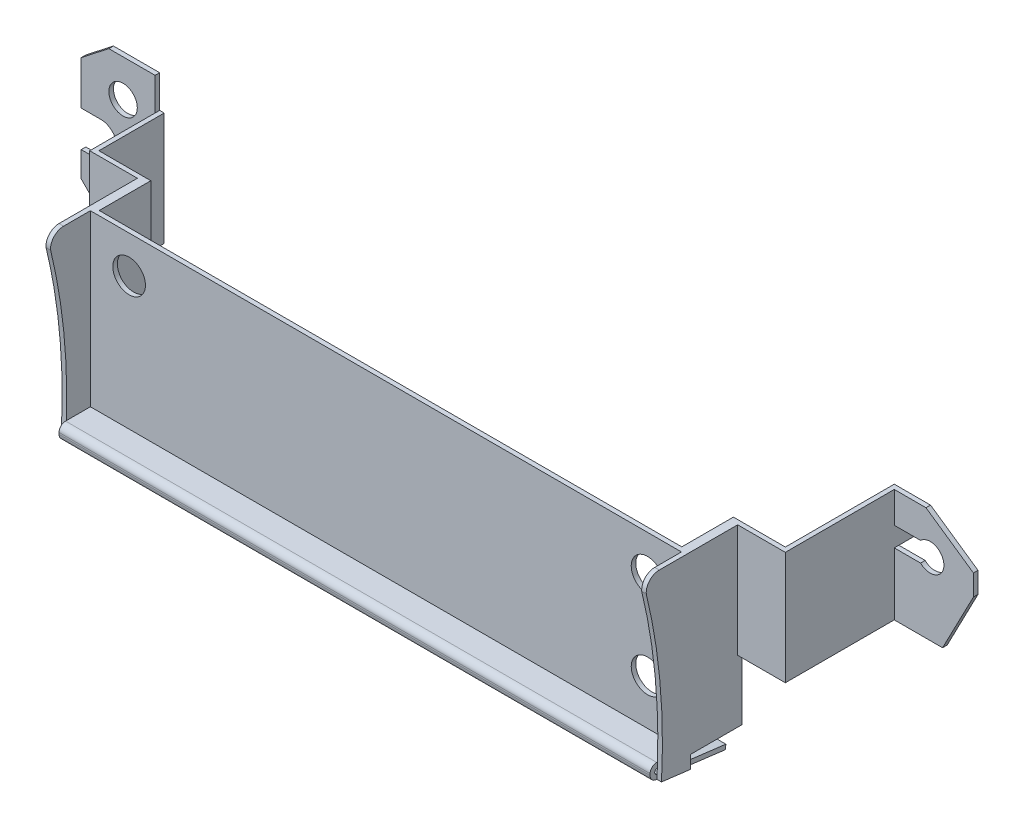
SolidWorks part; units mm, degrees
ref_plane "Front" through (0, 0, 0) normal (0, 0, 1) x (1, 0, 0)
ref_plane "Top" through (0, 0, 0) normal (0, 1, 0) x (1, 0, 0)
ref_plane "Right" through (0, 0, 0) normal (1, 0, 0) x (0, 0, -1)
sketch "Szkic1" plane through (0, 0, 0) normal (0, 0, 1) x (1, 0, 0)
  line L0 (-36.3541, -25.4134) -> (54.1459, -25.4134)
  line L1 (8.8959, -25.4134) -> (8.8959, 3.5933) construction
  line L2 (-36.3541, 0.5866) -> (54.1459, 0.5866)
  line L3 (-36.3541, 0.5866) -> (-36.3541, -25.4134)
  line L4 (54.1459, 0.5866) -> (54.1459, -25.4134)
  dimension "D1" = 26
  dimension "D3" = 90.5
  dimension "D2" = 26
  dimension "D4" = 90.5
  dimension "D5" = 90
  dimension "D6" = 90
extrude "Dodanie-wyciągnięcie1" add sketch "Szkic1" along normal blind 0.7
sketch "Szkic3" plane through (-36.3541, 0, 0) normal (-1, 0, 0) x (0, 0, 1)
  line L0 (0.7, -25.4134) -> (5.5, -25.4134) construction
  line L1 (0.7, -25.4134) -> (0.7, -28.153) construction
  line L2 (5.5, -26.4134) -> (5.5, -26.6702)
  line L3 (4.624, -27.6625) -> (-6.0104, -28.9918)
  line L4 (-6.0104, -28.9918) -> (-6.0972, -28.2972)
  line L5 (4.8, -26.598) -> (4.8, -26.6355)
  line L6 (-6.0972, -28.2972) -> (4.4976, -26.9779)
  line L7 (4.455, -26.253) -> (0, -26.253)
  line L8 (0, -26.253) -> (0, -25.4134)
  line L9 (0, -25.4134) -> (4.5, -25.4134)
  arc A0 (4.5, -25.4134) -> (5.5, -26.4134) centre (4.5, -26.4134) cw
  arc A1 (5.5, -26.6702) -> (4.624, -27.6625) centre (4.5, -26.6702) cw
  arc A2 (4.8, -26.6355) -> (4.4976, -26.9779) centre (4.455, -26.6355) cw
  arc A3 (4.8, -26.598) -> (4.455, -26.253) centre (4.455, -26.598) ccw
  dimension "D1" = 90
  dimension "D2" = 1
  dimension "D3" = 0.345
extrude "Dodanie-wyciągnięcie2" add sketch "Szkic3" against normal up to surface (90.5 mm away) separate body up to face at (54.1459, -12.4134, 0.35)
sketch "Szkic4" plane through (54.1459, 0, 0) normal (1, 0, 0) x (0, 0, -1)
  line L2 (0, 0.5866) -> (-4.7969, 0.5866)
  line L3 (0, 0.5866) -> (0, -28.2405)
  line L4 (-4.4693, -27.6819) -> (0, -28.2405)
  arc A0 (-6.7876, -1.6062) -> (-4.7969, 0.5866) centre (-4.7969, -1.4134) cw
  spline S0 degree 3 poles (-4.4693, -27.6819) (-4.4425, -27.2049) (-4.0104, -18.29) (-4.8511, -9.6107) (-6.7876, -1.6062) knots -0.045929 -0.045929 -0.045929 -0.045929 0 0.813756 0.813756 0.813756 0.813756
  dimension "D1" = 2
extrude "Dodanie-wyciągnięcie3" add sketch "Szkic4" along normal blind 0.7
sketch "Szkic8" plane through (-36.3541, 0, 0) normal (-1, 0, 0) x (0, 0, 1)
  line L1 (4.4693, -27.6819) -> (0, -28.2405)
  line L2 (4.7969, 0.5866) -> (0, 0.5866)
  line L3 (0, 0.5866) -> (0, -28.2405)
  arc A1 (6.7876, -1.6062) -> (4.7969, 0.5866) centre (4.7969, -1.4134) ccw
  spline S1 degree 3 poles (4.4693, -27.6819) (4.4425, -27.2049) (4.0104, -18.29) (4.8511, -9.6107) (6.7876, -1.6062) knots -0.045929 -0.045929 -0.045929 -0.045929 0 0.813756 0.813756 0.813756 0.813756
extrude "Dodanie-wyciągnięcie4" add sketch "Szkic8" along normal blind 0.7
sketch "Szkic9" plane through (0, 0, 0) normal (0, 0, -1) x (-1, 0, 0)
  line L0 (-54.8459, 0.5866) -> (-54.8459, -26.253)
  line L1 (37.0541, 0.5866) -> (37.0541, -26.253)
  line L2 (-53.4959, 0.5866) -> (-53.4959, -26.253)
  line L3 (-54.1459, -26.253) -> (36.3541, -26.253) construction
  line L4 (-53.4959, -26.253) -> (-54.8459, -26.253)
  line L5 (-54.8459, -28.2405) -> (-54.8459, 0.5866) construction
  line L6 (35.7041, 0.5866) -> (37.0541, 0.5866)
  line L7 (-54.8459, 0.5866) -> (-53.4959, 0.5866)
  line L10 (35.7041, -26.253) -> (37.0541, -26.253)
  line L11 (35.7041, -26.253) -> (35.7041, 0.5866)
extrude "Dodanie-wyciągnięcie5" add sketch "Szkic9" along normal blind 7.9
sketch "Szkic11" plane through (0, 0.5866, 0) normal (0, 1, 0) x (1, 0, 0)
  line L0 (-37.0541, 7.9) -> (-37.0541, 7.2)
  line L1 (-37.0541, 7.2) -> (-44.3541, 7.2)
  line L2 (-44.3541, 7.2) -> (-44.3541, 17.2)
  line L3 (-43.6541, 7.9) -> (-37.0541, 7.9)
  line L4 (-43.6541, 7.9) -> (-43.6541, 17.9)
  line L5 (-55.6541, 17.2) -> (-44.3541, 17.2)
  line L6 (-43.6541, 17.9) -> (-55.6541, 17.9)
  line L7 (-55.6541, 17.9) -> (-55.6541, 17.2)
  dimension "D1" = 10
  dimension "D2" = 11.3
extrude "Dodanie-wyciągnięcie6" add sketch "Szkic11" against normal blind 17.3
sketch "Szkic12" plane through (0, 0.5866, 0) normal (0, 1, 0) x (1, 0, 0)
  line L0 (54.8459, 7.9) -> (54.8459, 7.2)
  line L1 (62.1459, 7.2) -> (54.8459, 7.2)
  line L3 (54.8459, 7.9) -> (61.4459, 7.9)
  line L8 (74.2659, 24.58) -> (74.2659, 23.88)
  line L9 (61.4459, 24.58) -> (74.2659, 24.58)
  line L10 (74.2659, 23.88) -> (62.1459, 23.88)
  line L11 (62.1459, 7.2) -> (62.1459, 23.88)
  line L12 (61.4459, 7.9) -> (61.4459, 24.58)
  dimension "D1" = 12.82
  dimension "D2" = 16.68
  dimension "D3" = 0.7
  dimension "D4" = 16.68
extrude "Dodanie-wyciągnięcie7" add sketch "Szkic12" against normal blind 17.3
sketch "Szkic13" plane through (0, 0, -23.88) normal (0, 0, 1) x (1, 0, 0)
  line L0 (74.2459, -15.1844) -> (74.2459, 4.2987) construction
  line L1 (61.4459, -16.7134) -> (61.4459, 0.5866) construction
  line L2 (76.2499, -4.4134) -> (92.0698, -4.4134) construction
  line L3 (62.1459, 0.5866) -> (74.2659, 0.5866) construction
  line L4 (67.0047, 0.5866) -> (75.4895, -5.2721)
  line L5 (69.5395, -16.7134) -> (76.2499, -16.7134)
  line L6 (76.2499, -16.7134) -> (76.2499, 0.5866)
  line L7 (69.5395, -16.7134) -> (75.4895, -5.2721)
  line L8 (67.0047, 0.5866) -> (76.2499, 0.5866)
  line L10 (62.1459, -4.1634) -> (66.1762, -4.1634)
  line L11 (62.1459, -4.1634) -> (62.1459, -7.1634)
  line L13 (62.1459, -7.1634) -> (66.1762, -7.1634)
  line L14 (69.7459, -1.3062) -> (69.7459, 6.074) construction
  line L15 (62.1459, -5.6634) -> (70.5807, -5.6634) construction
  line L16 (67.6459, -5.6634) -> (69.7459, -5.6634) construction
  circle A0 centre (74.2459, -4.4134) radius 3.25 construction
  arc A1 (66.1762, -7.1634) -> (66.1762, -4.1634) centre (67.6459, -5.6634) ccw
  dimension "D3" = 4.75
  dimension "D1" = 12.8
  dimension "D2" = 5
  dimension "D4" = 3
  dimension "D5" = 7.6
extrude "Wytnij-wyciągnięcie1" cut sketch "Szkic13" against normal up to next
sketch "Szkic14" plane through (0, 0, -24.58) normal (0, 0, -1) x (-1, 0, 0)
  line L0 (-62.1459, -4.1634) -> (-61.4459, -4.1634)
  line L1 (-61.4459, -16.7134) -> (-61.4459, 0.5866) construction
  line L2 (-61.4459, -4.1634) -> (-61.4459, -7.1634)
  line L3 (-62.1459, -7.1634) -> (-62.1459, -4.1634)
  line L4 (-62.1459, -7.1634) -> (-61.4459, -7.1634)
extrude "Dodanie-wyciągnięcie8" add sketch "Szkic14" along normal blind 3.15
sketch "Szkic17" plane through (0, 0, -17.2) normal (0, 0, 1) x (1, 0, 0)
  line L0 (-44.3533, 0.5421) -> (-55.6541, 0.5866)
  line L1 (-55.6541, 0.5866) -> (-55.6541, 5.5866)
  line L2 (-55.6541, 5.5866) -> (-44.3533, 5.5866)
  line L3 (-44.3533, 5.5866) -> (-44.3533, 0.5421)
extrude "Dodanie-wyciągnięcie9" add sketch "Szkic17" against normal up to surface (0.7 mm away) up to face at (-49.6541, -8.0634, -17.9)
sketch "Szkic18" plane through (0, 0, -17.2) normal (0, 0, 1) x (1, 0, 0)
  line L0 (-51.4241, 5.5866) -> (-55.6541, 2.2866)
  line L1 (-51.4241, 5.5866) -> (-55.6541, 5.5866)
  line L2 (-55.6541, 5.5866) -> (-55.6541, 2.2866)
  line L3 (-55.6541, -4.4134) -> (-52.6541, -4.4134)
  line L4 (-55.6541, -16.7134) -> (-55.6541, 5.5866) construction
  line L5 (-44.3533, 5.5866) -> (-55.6541, 5.5866) construction
  line L6 (-55.6541, -9.9134) -> (-52.6541, -9.9134)
  line L7 (-50.1541, -6.9134) -> (-50.1541, -7.4134)
  line L8 (-46.3544, 2.0866) -> (-52.3533, 2.0866) construction
  line L9 (-51.4241, -1.0354) -> (-51.4241, 8.3952) construction
  line L10 (-51.4241, -0.0884) -> (-47.5597, -0.0884) construction
  line L11 (-49.2491, 2.0866) -> (-49.2491, -0.9265) construction
  line L12 (-55.6541, -9.9134) -> (-55.6541, -4.4134)
  arc A0 (-50.1541, -7.4134) -> (-52.6541, -9.9134) centre (-52.6541, -7.4134) cw
  arc A1 (-50.1541, -6.9134) -> (-52.6541, -4.4134) centre (-52.6541, -6.9134) ccw
  circle A2 centre (-49.2491, -0.0884) radius 2.175
  point P16 (-50.1541, -7.1634)
  dimension "D1" = 10
  dimension "D4" = 2.5
  dimension "D2" = 5.5
  dimension "D3" = 5.5
  dimension "D5" = 3.5
  dimension "D6" = 4.23
extrude "Wytnij-wyciągnięcie2" cut sketch "Szkic18" against normal up to surface (0.7 mm away) up to face at (-47.8871, -3.5134, -17.9)
sketch "Szkic19" plane through (0, 0, -17.2) normal (0, 0, 1) x (1, 0, 0)
  line L0 (-55.6541, -16.7134) -> (-55.6541, -18.7134)
  line L1 (-55.6541, -16.7134) -> (-47.1541, -16.7134)
  line L3 (-47.1541, -18.7134) -> (-55.6541, -18.7134)
  line L4 (-47.1541, -16.7134) -> (-47.1541, -18.7134)
extrude "Dodanie-wyciągnięcie10" add sketch "Szkic19" against normal up to surface (0.7 mm away) up to face at (-50.3566, -4.7519, -17.9)
sketch "Szkic21" plane through (0, 0, -17.2) normal (0, 0, 1) x (1, 0, 0)
  line L0 (-55.6541, -13.8134) -> (-50.7541, -18.7134)
  line L1 (-50.7541, -18.7134) -> (-55.6541, -18.7134)
  line L2 (-55.6541, -18.7134) -> (-55.6541, -13.8134)
extrude "Wytnij-wyciągnięcie3" cut sketch "Szkic21" against normal up to surface (0.7 mm away) up to face at (-49.9296, -6.6134, -17.9)
sketch "Szkic22" plane through (0, 0, -17.9) normal (0, 0, -1) x (-1, 0, 0)
  line L0 (47.1541, -18.7134) -> (47.1541, -18.0134)
  line L1 (47.1541, -18.7134) -> (47.1541, -16.7134) construction
  line L3 (47.1541, -18.7134) -> (50.7541, -18.7134)
  line L4 (47.1541, -18.0134) -> (50.7541, -18.0134)
  line L5 (50.7541, -18.7134) -> (50.7541, -18.0134)
extrude "Dodanie-wyciągnięcie11" add sketch "Szkic22" along normal blind 3.3
sketch "Szkic23" plane through (0, 0, 0) normal (0, 0, -1) x (-1, 0, 0)
  line L0 (30.4241, -18.4369) -> (-56.6973, -18.4369) construction
  line L1 (-48.9509, -5.1019) -> (-48.9509, -23.1911) construction
  circle A0 centre (-48.9509, -5.1019) radius 2.5
  circle A1 centre (30.4241, -5.1019) radius 2.5
  circle A3 centre (-48.9509, -18.4369) radius 2.5
extrude "Wytnij-wyciągnięcie4" cut sketch "Szkic23" against normal up to surface (0.7 mm away) up to face at (8.8959, -12.4134, 0.7)
